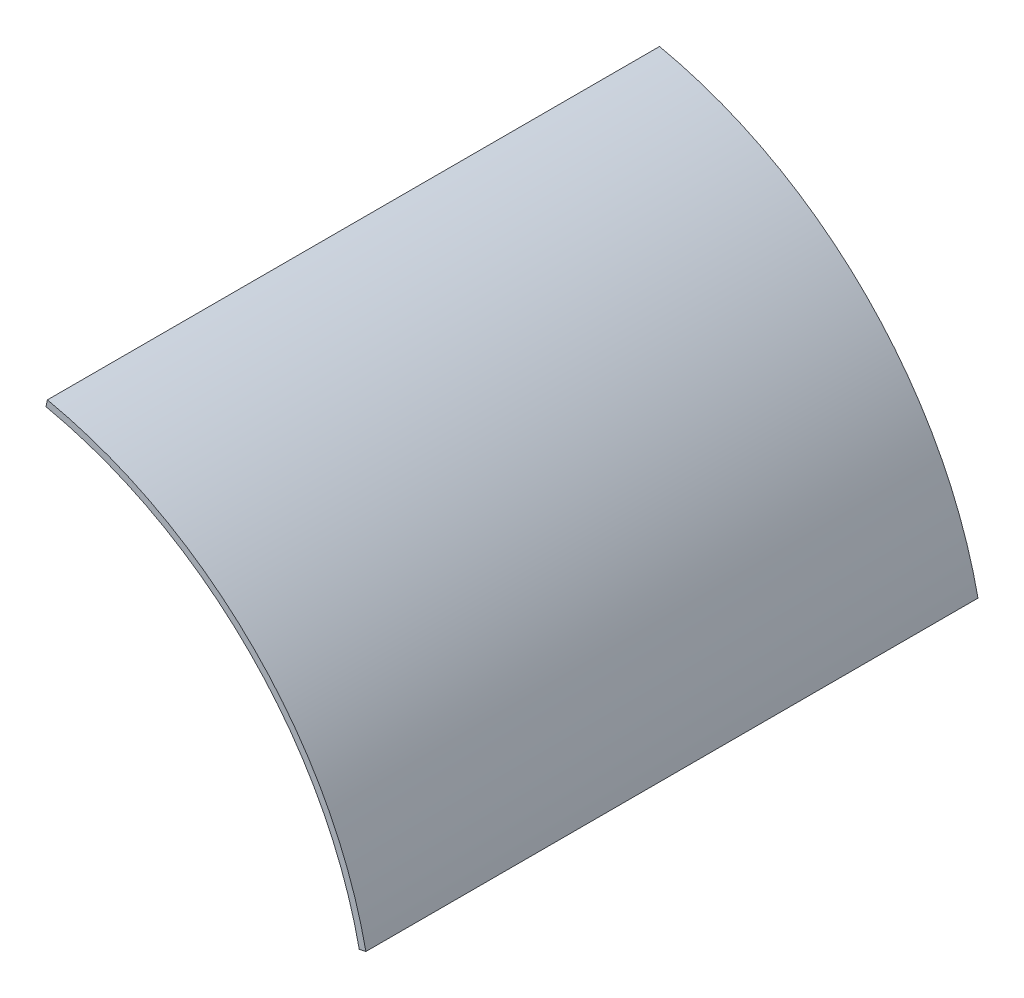
SolidWorks part; units mm, degrees
material "POM Acetal Copolymer"
ref_plane "Alzado" through (0, 0, 0) normal (0, 0, 1) x (1, 0, 0)
ref_plane "Planta" through (0, 0, 0) normal (0, 1, 0) x (1, 0, 0)
ref_plane "Vista lateral" through (0, 0, 0) normal (1, 0, 0) x (0, 0, -1)
sketch "Croquis1" plane through (0, 0, 0) normal (0, 0, 1) x (1, 0, 0)
  line L0 (0, 0) -> (0, 58) construction
  line L1 (0, 0) -> (58, 0) construction
  line L2 (0, 0) -> (29.7357, 6.3205) construction
  line L3 (0, 0) -> (6.3205, 29.7357) construction
  line L4 (6.3205, 29.7357) -> (6.2166, 29.2466)
  line L5 (29.7357, 6.3205) -> (29.2466, 6.2166)
  arc A0 (6.2166, 29.2466) -> (29.2466, 6.2166) centre (0, 0) cw
  arc A1 (29.7357, 6.3205) -> (6.3205, 29.7357) centre (0, 0) ccw
  dimension "D1" = 29.9
  dimension "D2" = 0.5
  dimension "D3" = 12
  dimension "D4" = 12
extrude "Saliente-Extruir1" add sketch "Croquis1" along normal blind 45
